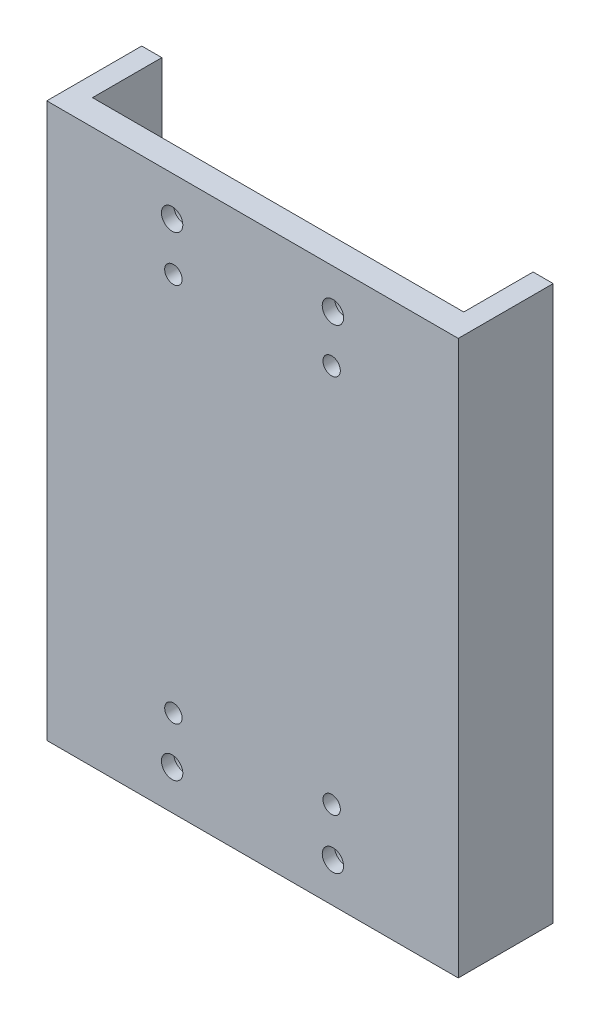
SolidWorks part; units mm, degrees
material "6061-T6 (SS)"
ref_plane "Front Plane" through (0, 0, 0) normal (0, 0, 1) x (1, 0, 0)
ref_plane "Top Plane" through (0, 0, 0) normal (0, 1, 0) x (1, 0, 0)
ref_plane "Right Plane" through (0, 0, 0) normal (1, 0, 0) x (0, 0, -1)
sketch "Sketch1" plane through (0, 0, 0) normal (0, 1, 0) x (1, 0, 0)
  line L0 (58.65, 30) -> (65, 30)
  line L1 (-65, 0) -> (65, 0)
  line L2 (-65, 0) -> (-65, 30)
  line L3 (-65, 30) -> (-58.65, 30)
  line L4 (65, 0) -> (65, 30)
  line L6 (58.65, 30) -> (58.65, 8.0907)
  line L7 (58.65, 8.0907) -> (-58.65, 8.0907)
  line L8 (-58.65, 30) -> (-58.65, 8.0907)
  dimension "D1" = 130
  dimension "D2" = 30
  dimension "D3" = 6.35
extrude "Boss-Extrude1" add sketch "Sketch1" along normal mid plane 175
hole_wizard "CBORE for 1/4 Binding Head Machine Screw1" positions "Sketch2" profile "Sketch3" counterbore size "1/4" standard "ANSI Inch" end condition through all
sketch "Sketch2" plane through (0, 0, -8.0907) normal (0, 0, -1) x (-1, 0, 0)
  line L1 (-25.4, 75) -> (25.4, 75)
  line L2 (-25.4, 75) -> (-25.4, -75)
  line L3 (-25.4, -75) -> (25.4, -75)
  line L4 (25.4, 75) -> (25.4, -75)
  line L5 (-25.4, 75) -> (25.4, -75) construction
  line L6 (-25.4, -75) -> (25.4, 75) construction
  point P0 (-25.4, 75)
  point P4 (25.4, -75)
  point P114 (-25.4, -75)
  point P115 (25.4, 75)
  dimension "D1" = 50.8
  dimension "D2" = 150
sketch "Sketch3" plane through (25.4, 75, -8.0907) normal (1, 0, 0) x (0, 1, 0)
  line L0 (0, 0) -> (0, 8.0907)
  line L1 (0, 8.0907) -> (3.3782, 8.0907)
  line L3 (3.3782, 8.0907) -> (3.3782, 4.191)
  line L4 (3.3782, 4.191) -> (7.1437, 4.191)
  line L5 (7.1437, 4.191) -> (7.1437, 0)
  line L7 (7.1437, 0) -> (0, 0)
  line L11 (0, -6.35) -> (0, 107.95) construction
  dimension "Thru Hole Dia." = 6.7564
  dimension "Thru Hole Depth" = 8.0907
  dimension "C'Bore Dia." = 14.2875
  dimension "C'Bore Depth" = 4.191
hole_wizard "CBORE for M5 Hex Head Bolt1" positions "Sketch4" profile "Sketch5" counterbore size "M5" standard "ANSI Metric" end condition through all
sketch "Sketch4" plane through (0, 0, -8.0907) normal (0, 0, -1) x (-1, 0, 0)
  line L1 (-25, 60) -> (25, 60)
  line L2 (-25, 60) -> (-25, -60)
  line L3 (-25, -60) -> (25, -60)
  line L4 (25, 60) -> (25, -60)
  line L5 (-25, 60) -> (25, -60) construction
  line L6 (-25, -60) -> (25, 60) construction
  point P2 (25, -60)
  point P101 (-25, 60)
  point P102 (-25, -60)
  point P103 (25, 60)
  dimension "D1" = 50
  dimension "D2" = 120
sketch "Sketch5" plane through (-25, -60, -8.0907) normal (1, 0, 0) x (0, 1, 0)
  line L0 (0, 0) -> (0, 8.0907)
  line L1 (0, 8.0907) -> (2.75, 8.0907)
  line L3 (2.75, 8.0907) -> (2.75, 3.58)
  line L4 (2.75, 3.58) -> (6.12, 3.58)
  line L5 (6.12, 3.58) -> (6.12, 0)
  line L7 (6.12, 0) -> (0, 0)
  line L11 (0, -6.35) -> (0, 107.95) construction
  dimension "Thru Hole Dia." = 5.5
  dimension "Thru Hole Depth" = 8.0907
  dimension "C'Bore Dia." = 12.24
  dimension "C'Bore Depth" = 3.58
